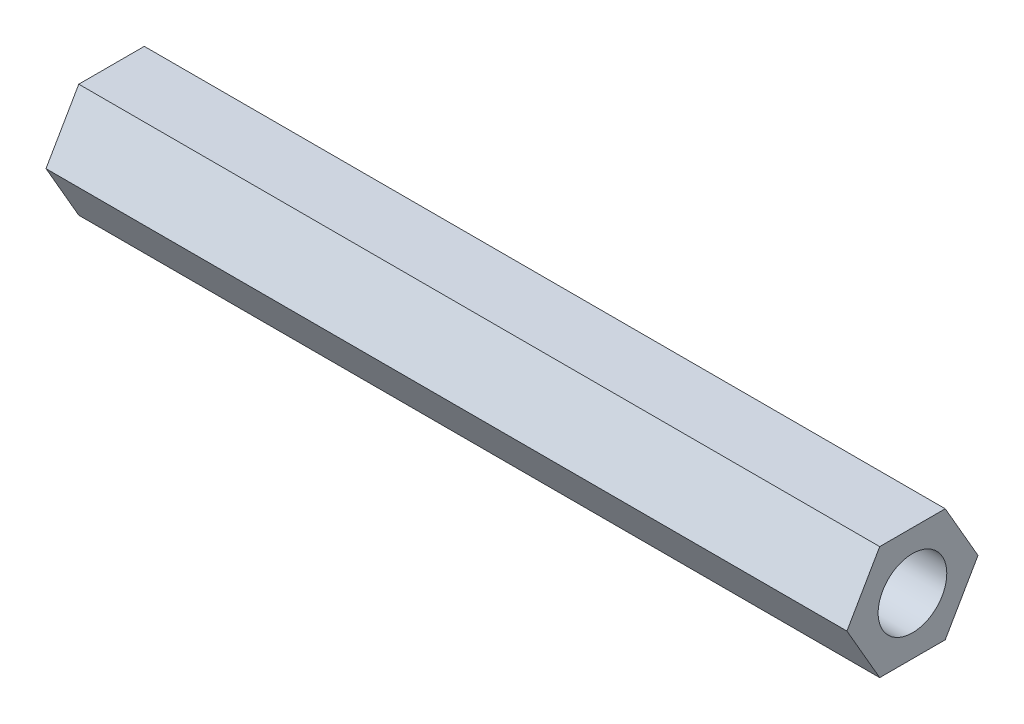
SolidWorks part; units mm, degrees
ref_plane "Front Plane" through (0, 0, 0) normal (0, 0, 1) x (1, 0, 0)
ref_plane "Top Plane" through (0, 0, 0) normal (0, 1, 0) x (1, 0, 0)
ref_plane "Right Plane" through (0, 0, 0) normal (1, 0, 0) x (0, 0, -1)
ref_plane "Plane1" through (0, 0, 0) normal (-1, 0, 0) x (0, -1, 0)
sketch "Sketch1" plane through (0, 0, 0) normal (-1, 0, 0) x (0, -1, 0)
  line L0 (7.874, -4.5461) -> (7.874, 4.5461)
  line L1 (7.874, 4.5461) -> (0, 9.0921)
  line L2 (0, 9.0921) -> (-7.874, 4.5461)
  line L3 (-7.874, 4.5461) -> (-7.874, -4.5461)
  line L4 (-7.874, -4.5461) -> (0, -9.0921)
  line L5 (0, -9.0921) -> (7.874, -4.5461)
  circle A0 centre (0, 0) radius 4.7625
extrude "Boss-Extrude1" add sketch "Sketch1" against normal blind 111.125
